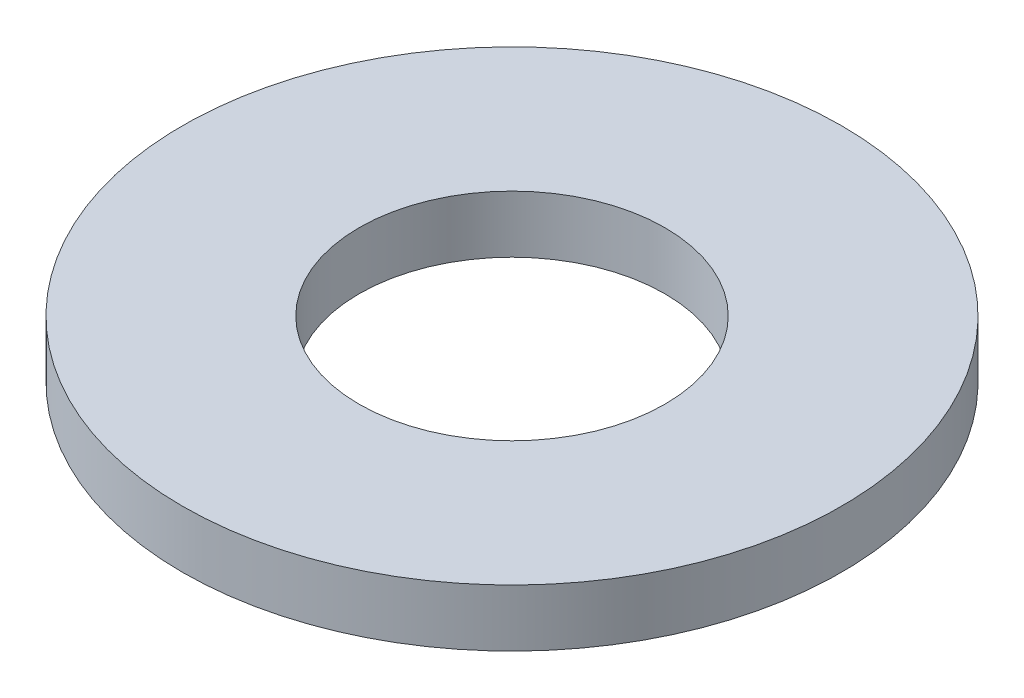
SolidWorks part; units mm, degrees
ref_plane "Front Plane" through (0, 0, 0) normal (0, 0, 1) x (1, 0, 0)
ref_plane "Top Plane" through (0, 0, 0) normal (0, 1, 0) x (1, 0, 0)
ref_plane "Right Plane" through (0, 0, 0) normal (1, 0, 0) x (0, 0, -1)
sketch "Sketch1" plane through (0, 0, 0) normal (0, 1, 0) x (1, 0, 0)
  circle A0 centre (0, 0) radius 5.5562
  dimension "OD" = 11.1125
extrude "Boss-Extrude1" add sketch "Sketch1" along normal blind 0.9652
sketch "Sketch5" plane through (0, 0.9652, 0) normal (0, 1, 0) x (-1, 0, 0)
  circle A0 centre (0, 0) radius 2.5781
  dimension "ID" = 5.1562
extrude "Cut-Extrude1" cut sketch "Sketch5" against normal through all
